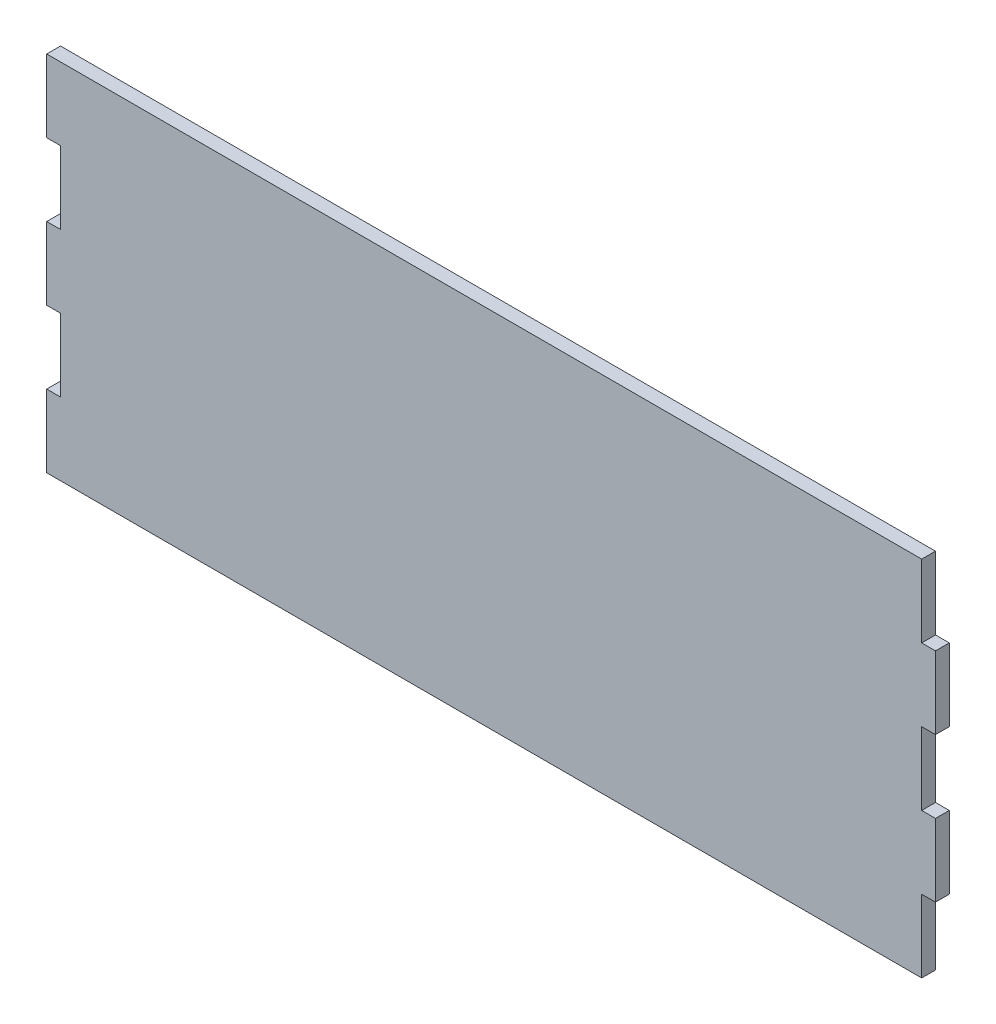
SolidWorks part; units mm, degrees
material "1060 Alloy"
ref_plane "Front Plane" through (0, 0, 0) normal (0, 0, 1) x (1, 0, 0)
ref_plane "Top Plane" through (0, 0, 0) normal (0, 1, 0) x (1, 0, 0)
ref_plane "Right Plane" through (0, 0, 0) normal (1, 0, 0) x (0, 0, -1)
sketch "Sketch1" plane through (0, 0, 0) normal (0, 0, 1) x (1, 0, 0)
  line L0 (311.15, 127) -> (311.15, 101.6) construction
  line L1 (0, 0) -> (622.3, 0) construction
  line L2 (0, 0) -> (0, 127) construction
  line L3 (0, 127) -> (622.3, 127) construction
  line L4 (622.3, 0) -> (622.3, 127) construction
  line L5 (617.474, 25.4) -> (617.474, 0)
  line L6 (311.15, 127) -> (617.474, 127)
  line L7 (311.15, 127) -> (311.15, 101.6)
  line L8 (311.15, 0) -> (617.474, 0)
  line L9 (617.474, 127) -> (617.474, 101.6)
  line L10 (617.474, 101.6) -> (622.3, 101.6)
  line L11 (311.15, 76.2) -> (311.15, 50.8) construction
  line L12 (617.474, 76.2) -> (622.3, 76.2)
  line L13 (622.3, 101.6) -> (622.3, 76.2)
  line L14 (622.3, 50.8) -> (617.474, 50.8)
  line L15 (622.3, 50.8) -> (622.3, 25.4)
  line L16 (622.3, 25.4) -> (617.474, 25.4)
  line L17 (311.15, 25.4) -> (311.15, 0) construction
  line L18 (617.474, 76.2) -> (617.474, 50.8)
  line L19 (311.15, 101.6) -> (315.976, 101.6)
  line L21 (311.15, 76.2) -> (315.976, 76.2)
  line L22 (315.976, 101.6) -> (315.976, 76.2)
  line L23 (311.15, 50.8) -> (315.976, 50.8)
  line L25 (311.15, 25.4) -> (315.976, 25.4)
  line L26 (315.976, 50.8) -> (315.976, 25.4)
  line L27 (311.15, 76.2) -> (311.15, 50.8)
  line L28 (311.15, 25.4) -> (311.15, 0)
  dimension "D1" = 127
  dimension "D2" = 622.3
  dimension "D3" = 4.826
  dimension "D4" = 4.826
extrude "Boss-Extrude1" add sketch "Sketch1" along normal blind 4.826
equation "\"sheet width\"= .19"
equation "\"width\"= 24.5"
equation "\"length\"= 34.5"
equation "\"standoff hole size\"= .5"
equation "\"ground clearence\"= 3"
equation "\"small drive pulley\"= 74.55mm"
equation "\"large drive pulley\"= 150.95mm"
equation "\"drive axle hole size\"= .5"
equation "\"front pulley clearence\"= 1"
equation "\"center support location\"= 19"
equation "\"inner to outer wall size\"= 3.75"
equation "\"D2@Sketch1\"=\"width\""
equation "\"D3@Sketch1\"=\"sheet width\""
equation "\"D4@Sketch1\"=\"sheet width\""
equation "\"D1@Boss-Extrude1\"=\"sheet width\""
